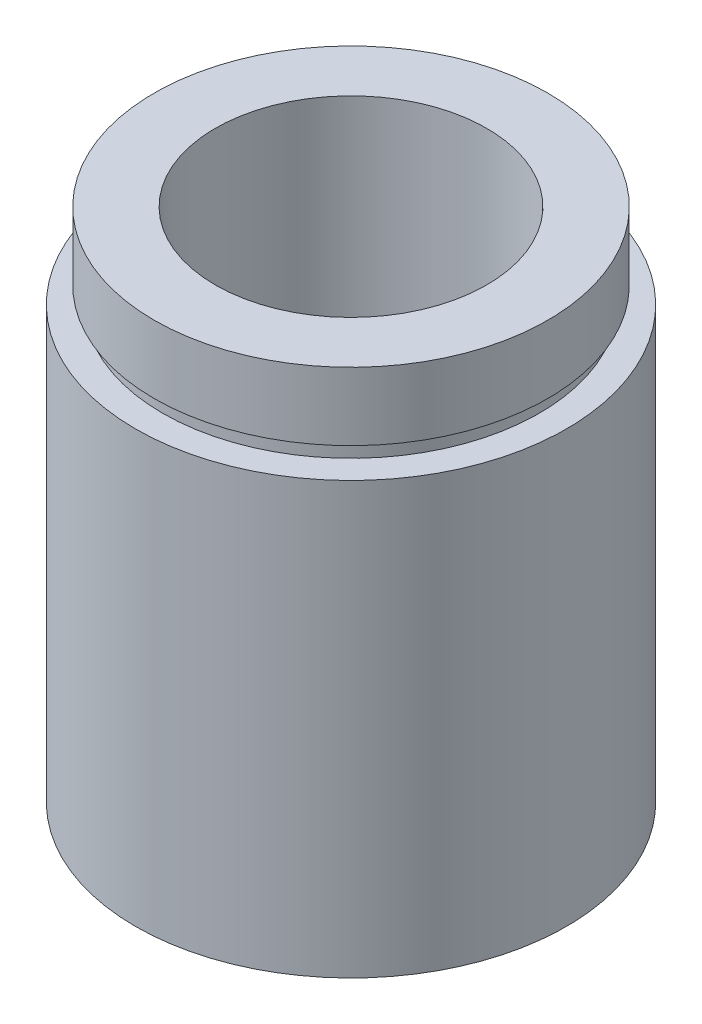
SolidWorks part; units mm, degrees
ref_plane "前视基准面" through (0, 0, 0) normal (0, 0, 1) x (1, 0, 0)
ref_plane "上视基准面" through (0, 0, 0) normal (0, 1, 0) x (1, 0, 0)
ref_plane "右视基准面" through (0, 0, 0) normal (1, 0, 0) x (0, 0, -1)
sketch "草图1" plane through (0, 0, 0) normal (0, 0, 1) x (1, 0, 0)
  line L0 (0, 161.3762) -> (0, 0) construction
  line L1 (141.7365, 0) -> (-131.7984, 0) construction
  line L2 (11.1, 0) -> (11.1, 4.5)
  line L3 (11.7, 4.5) -> (11.7, 5.5)
  line L4 (11.1, 4.5) -> (11.7, 4.5)
  line L5 (8, 5.5) -> (8, 30.4)
  line L6 (11.7, 5.5) -> (8, 5.5)
  line L7 (12.7, 0) -> (12.7, 25.4)
  line L8 (11.1, 0) -> (12.7, 0)
  line L9 (11.1, 25.4) -> (11.1, 26.4)
  line L10 (12.7, 25.4) -> (11.1, 25.4)
  line L11 (11.6, 26.4) -> (11.6, 30.4)
  line L12 (11.1, 26.4) -> (11.6, 26.4)
  line L13 (11.6, 30.4) -> (8, 30.4)
  point P12 (8, 81.5721)
  dimension "D1" = 11.1
  dimension "D2" = 4.5
  dimension "D3" = 11.7
  dimension "D4" = 8
  dimension "D5" = 11.1
  dimension "D6" = 11.6
  dimension "D7" = 5
  dimension "D8" = 1
  dimension "D9" = 12.7
  dimension "D10" = 1
  dimension "D11" = 25.4
revolve "旋转1" add sketch "草图1" angle 360 about L0
cosmetic thread "装饰螺纹线1" parameters "D2"=23.2
cosmetic thread "装饰螺纹线2" parameters "D2"=17
cosmetic thread "装饰螺纹线3" parameters "D2"=23.19
